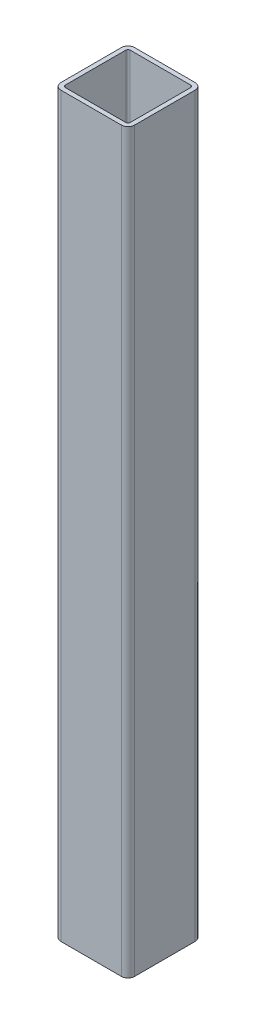
SolidWorks part; units mm, degrees
material "Default"
ref_plane "Front Plane" through (0, 0, 0) normal (0, 0, 1) x (1, 0, 0)
ref_plane "Top Plane" through (0, 0, 0) normal (0, 1, 0) x (1, 0, 0)
ref_plane "Right Plane" through (0, 0, 0) normal (1, 0, 0) x (0, 0, -1)
sketch "Sketch1" plane through (0, 0, 0) normal (0, 0, 1) x (1, 0, 0)
  line L0 (0, 0) -> (0, 500)
  dimension "D1" = 500
other "Ptr ASTM A500 GRADO B(1)"
ref_plane "Plane1" through (0, 0, 0) normal (0, 1, 0) x (-1, 0, 0)
sketch "Sketch11" plane through (0, 0, 0) normal (0, 1, 0) x (-1, 0, 0)
  line L6 (20.5, 25) -> (-20.5, 25)
  line L11 (25, 20.5) -> (25, -20.5)
  line L13 (20.5, -25) -> (-20.5, -25)
  line L30 (-25, 20.5) -> (-25, -20.5)
  line L31 (25, 25) -> (-25, -25) construction
  line L32 (25, -25) -> (-25, 25) construction
  line L33 (20.5, 22) -> (-20.5, 22)
  line L34 (22, 20.5) -> (22, -20.5)
  line L35 (20.5, -22) -> (-20.5, -22)
  line L36 (-22, 20.5) -> (-22, -20.5)
  line L37 (22, 22) -> (-22, -22) construction
  line L38 (22, -22) -> (-22, 22) construction
  arc A0 (20.5, 22) -> (22, 20.5) centre (20.5, 20.5) cw
  arc A1 (22, -20.5) -> (20.5, -22) centre (20.5, -20.5) cw
  arc A2 (-20.5, -22) -> (-22, -20.5) centre (-20.5, -20.5) cw
  arc A3 (-20.5, 22) -> (-22, 20.5) centre (-20.5, 20.5) ccw
  arc A4 (25, -20.5) -> (20.5, -25) centre (20.5, -20.5) cw
  arc A5 (-20.5, -25) -> (-25, -20.5) centre (-20.5, -20.5) cw
  arc A6 (20.5, 25) -> (25, 20.5) centre (20.5, 20.5) cw
  arc A7 (-20.5, 25) -> (-25, 20.5) centre (-20.5, 20.5) ccw
  point P0 (0, 0)
  point P1 (0, 0)
  point P6 (0, 0)
  point P8 (0, 0)
  point P37 (0, 0)
  dimension "D4" = 1.5
  dimension "D5" = 4.5
  dimension "D1" = 50
  dimension "D2" = 3
  dimension "D3" = 3
equation "\"largo viga enterrada\"= .5m"
equation "\"D1@Sketch1\"=\"largo viga enterrada\""
